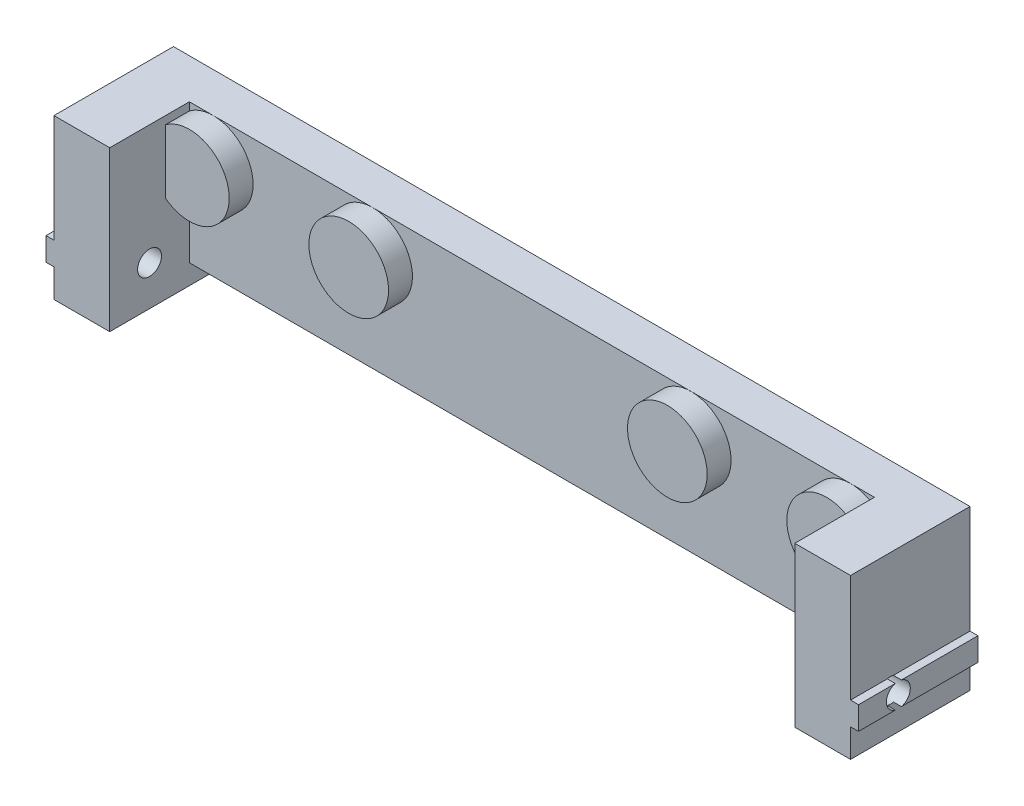
SolidWorks part; units mm, degrees
ref_plane "Front Plane" through (0, 0, 0) normal (0, 0, 1) x (1, 0, 0)
ref_plane "Top Plane" through (0, 0, 0) normal (0, 1, 0) x (1, 0, 0)
ref_plane "Right Plane" through (0, 0, 0) normal (1, 0, 0) x (0, 0, -1)
sketch "Sketch1" plane through (0, 0, 0) normal (0, 0, 1) x (1, 0, 0)
  line L0 (-50, 0) -> (50, 0)
  line L1 (-50, 0) -> (-50, 3.55)
  line L2 (-50, 3.55) -> (-51, 3.55)
  line L3 (-51, 3.55) -> (-51, 6.45)
  line L4 (-51, 6.45) -> (-50, 6.45)
  line L7 (-50, 6.45) -> (-50, 20)
  line L8 (-50, 20) -> (50, 20)
  line L9 (50, 20) -> (50, 6.45)
  line L12 (50, 6.45) -> (51, 6.45)
  line L13 (51, 6.45) -> (51, 3.55)
  line L14 (51, 3.55) -> (50, 3.55)
  line L15 (50, 3.55) -> (50, 0)
  point P24 (0, 0)
  dimension "D1" = 100
  dimension "D2" = 3.55
  dimension "D3" = 2.9
  dimension "D4" = 1
  dimension "D5" = 20
extrude "Main" add sketch "Sketch1" along normal blind 15
sketch "Sketch2" plane through (0, 0, 15) normal (0, 0, 1) x (1, 0, 0)
  line L0 (-50, 0) -> (50, 0) construction
  line L1 (-43, 0) -> (43, 0)
  line L2 (-43, 0) -> (-43, 20)
  line L3 (-43, 20) -> (43, 20)
  line L4 (43, 0) -> (43, 20)
  line L5 (-50, 3.55) -> (-50, 0) construction
  line L6 (50, 0) -> (50, 3.55) construction
  line L7 (50, 20) -> (-50, 20) construction
  point P10 (50, 1.775)
  dimension "D1" = 7
  dimension "D2" = 7
extrude "TopExtrusion" cut sketch "Sketch2" against normal blind 10
sketch "Sketch5" plane through (0, 0, 5) normal (0, 0, 1) x (1, 0, 0)
  line L0 (-43, 0) -> (43, 0) construction
  circle A0 centre (-40, 15) radius 5
  circle A1 centre (-20, 15) radius 5
  circle A2 centre (20, 15) radius 5
  circle A3 centre (40, 15) radius 5
  dimension "D1" = 10
  dimension "D2" = 15
  dimension "D3" = 40
  dimension "D4" = 40
  dimension "D5" = 20
  dimension "D6" = 20
extrude "ReinforcementHoles" add sketch "Sketch5" along normal blind 3
sketch "Sketch3" plane through (0, 0, 0) normal (0, 0, 1) x (1, 0, 0)
  line L0 (-43, 0) -> (43, 0) construction
  circle A0 centre (-40, 15) radius 3
  circle A1 centre (20, 15) radius 3
  dimension "D1" = 6
  dimension "D4" = 60
  dimension "D2" = 15
  dimension "D3" = 40
extrude "Holes" cut sketch "Sketch3" along normal blind 5
mirror "Mirror1" about plane through (0, 0, 0) normal (1, 0, 0) of "Holes"
sketch "Sketch4" plane through (51, 0, 0) normal (1, 0, 0) x (0, 0, -1)
  line L0 (-15, 0) -> (0, 0) construction
  line L1 (-15, 3.55) -> (-15, 6.45) construction
  circle A0 centre (-10, 5) radius 1.5
  dimension "D1" = 5
  dimension "D3" = 3
  dimension "D2" = 5
extrude "FixHoles" cut sketch "Sketch4" against normal through all
sketch "Sketch6" plane through (0, 0, 5) normal (0, 0, 1) x (1, 0, 0)
  line L0 (-43, 0) -> (43, 0) construction
  line L1 (43, 2.5) -> (-43, 2.5)
  line L2 (43, 2.5) -> (43, 0)
  line L3 (43, 0) -> (-43, 0)
  line L4 (-43, 2.5) -> (-43, 0)
  line L5 (-43, 20) -> (-43, 0) construction
  line L6 (-43, 11) -> (-43, 0) construction
  line L7 (43, 0) -> (43, 20) construction
  line L8 (43, 0) -> (43, 11) construction
  dimension "D1" = 2.5
extrude "ForWindow" cut sketch "Sketch6" against normal through all
sketch "Sketch7" plane through (0, 2.5, 0) normal (0, -1, 0) x (-1, 0, 0)
  line L0 (-43, 0) -> (43, 0) construction
  line L1 (43, 0) -> (43, -5) construction
  line L2 (-43, 0) -> (-43, -5) construction
  circle A0 centre (36, -2.5) radius 1.25
  circle A1 centre (-36, -2.5) radius 1.25
  dimension "D1" = 2.5
  dimension "D2" = 2.5
  dimension "D3" = 7
  dimension "D4" = 7
extrude "Cut-Extrude2" cut sketch "Sketch7" against normal blind 10
